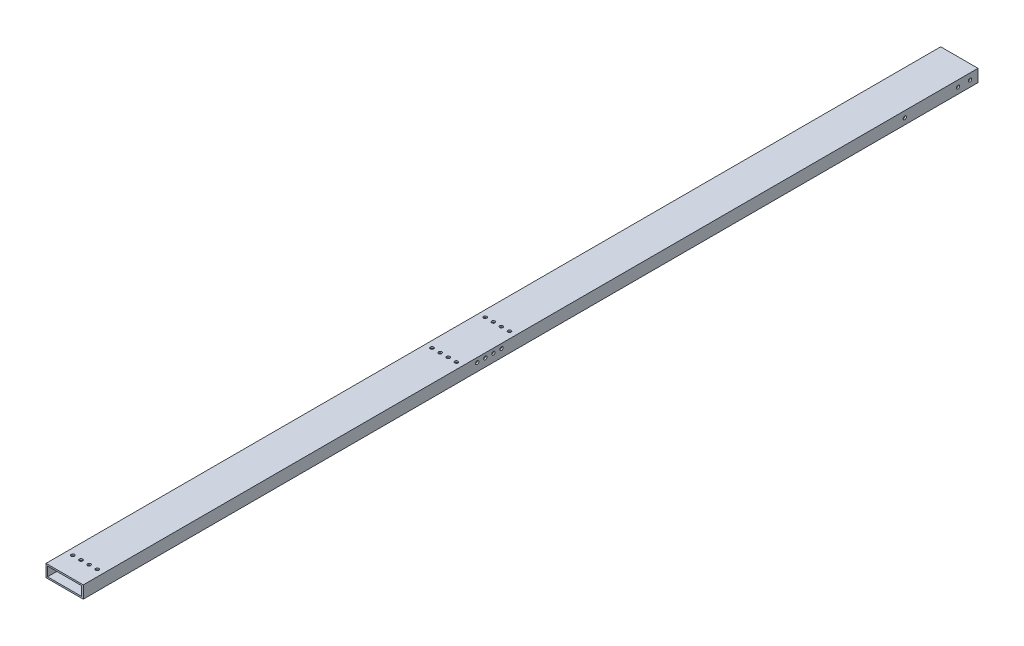
SolidWorks part; units mm, degrees
material "6061-T6 (SS)"
ref_plane "Front Plane" through (0, 0, 0) normal (0, 0, 1) x (1, 0, 0)
ref_plane "Top Plane" through (0, 0, 0) normal (0, 1, 0) x (1, 0, 0)
ref_plane "Right Plane" through (0, 0, 0) normal (1, 0, 0) x (0, 0, -1)
sketch "Sketch1" plane through (0, 0, 0) normal (0, 0, 1) x (1, 0, 0)
  line L0 (3.175, 3.175) -> (73.025, 3.175)
  line L1 (0, 0) -> (76.2, 0)
  line L2 (0, 0) -> (0, 25.4)
  line L3 (0, 25.4) -> (76.2, 25.4)
  line L4 (76.2, 0) -> (76.2, 25.4)
  line L5 (73.025, 3.175) -> (73.025, 22.225)
  line L6 (3.175, 22.225) -> (73.025, 22.225)
  line L7 (3.175, 3.175) -> (3.175, 22.225)
  dimension "D1" = 76.2
  dimension "D2" = 25.4
  dimension "D3" = 3.175
extrude "Boss-Extrude1" add sketch "Sketch1" along normal blind 1828.8
sketch "Sketch2" plane through (0, 25.4, 0) normal (0, 1, 0) x (1, 0, 0)
  line L0 (38.1, -1828.8) -> (38.1, 0) construction
  line L1 (76.2, -1828.8) -> (0, -1828.8) construction
  line L2 (76.2, 0) -> (0, 0) construction
sketch "Sketch3" plane through (0, 0, 0) normal (0, -1, 0) x (1, 0, 0)
  circle A0 centre (13.2131, 1787.1313) radius 3.3782
  circle A1 centre (29.8044, 1787.1313) radius 3.3782
  circle A2 centre (46.3956, 1787.1313) radius 3.3782
  circle A3 centre (62.9869, 1787.1313) radius 3.3782
  dimension "D1" = 6.7564
  dimension "D2" = 6.7564
  dimension "D3" = 6.7564
  dimension "D4" = 6.7564
extrude "Cut-Extrude1" cut sketch "Sketch3" against normal through all
sketch "Sketch4" plane through (76.2, 0, 0) normal (1, 0, 0) x (0, 0, -1)
  circle A0 centre (-1023.5909, 16.2687) radius 3.3782
  circle A1 centre (-1006.9996, 16.2687) radius 3.3782
  circle A2 centre (-990.4084, 16.2687) radius 3.3782
  circle A3 centre (-973.8171, 16.2687) radius 3.3782
  dimension "D1" = 6.7564
  dimension "D2" = 6.7564
  dimension "D3" = 6.7564
  dimension "D4" = 6.7564
extrude "Cut-Extrude2" cut sketch "Sketch4" against normal through all
sketch "Sketch5" plane through (0, 0, 0) normal (0, -1, 0) x (1, 0, 0)
  circle A0 centre (13.2131, 1053.0727) radius 3.3782
  circle A1 centre (29.8044, 1053.0727) radius 3.3782
  circle A2 centre (46.3956, 1053.0727) radius 3.3782
  circle A3 centre (62.9869, 1053.0727) radius 3.3782
  dimension "D1" = 6.7564
  dimension "D2" = 6.7564
  dimension "D3" = 6.7564
  dimension "D4" = 6.7564
extrude "Cut-Extrude3" cut sketch "Sketch5" against normal through all
sketch "Sketch6" plane through (0, 0, 0) normal (0, -1, 0) x (1, 0, 0)
  circle A0 centre (13.2131, 944.3353) radius 3.3782
  circle A1 centre (46.3956, 944.3353) radius 3.3782
  circle A2 centre (62.9869, 944.3353) radius 3.3782
  circle A3 centre (29.8044, 944.3353) radius 3.3782
  dimension "D1" = 6.7564
  dimension "D2" = 6.7564
  dimension "D3" = 6.7564
  dimension "D4" = 6.7564
extrude "Cut-Extrude4" cut sketch "Sketch6" against normal through all
sketch "Sketch7" plane through (76.2, 0, 0) normal (1, 0, 0) x (0, 0, -1)
  circle A0 centre (-16.2687, 12.7) radius 3.3782
  circle A1 centre (-40.8949, 12.7) radius 3.3782
  circle A2 centre (-149.6323, 12.7) radius 3.3782
  dimension "D1" = 6.7564
  dimension "D2" = 6.7564
  dimension "D3" = 6.7564
extrude "Cut-Extrude5" cut sketch "Sketch7" against normal through all
